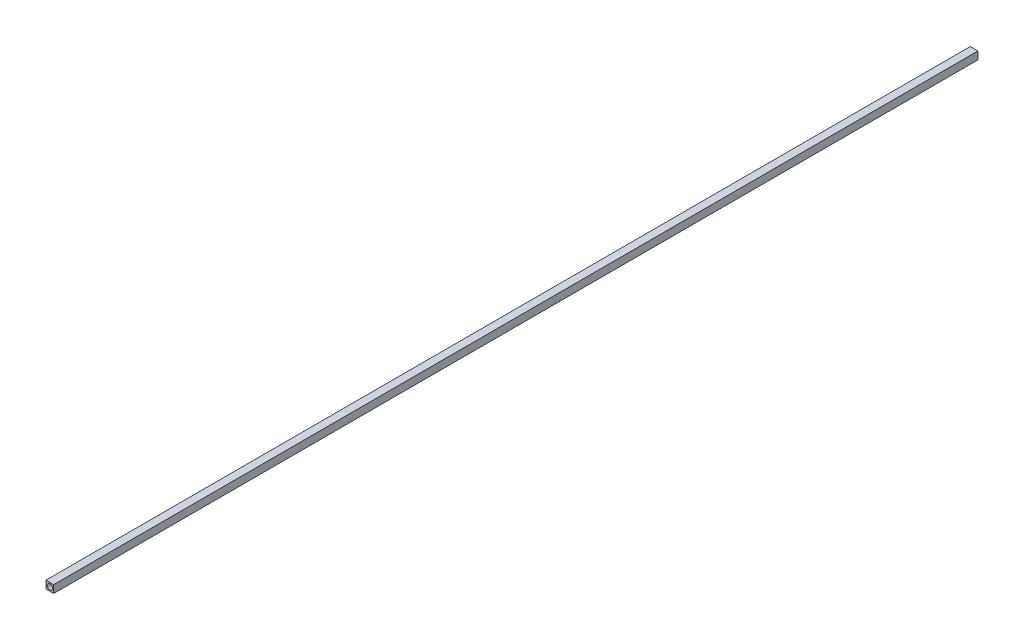
SolidWorks part; units mm, degrees
material "Uni Pultruded Tube"
ref_plane "Front Plane" through (0, 0, 0) normal (0, 0, 1) x (1, 0, 0)
ref_plane "Top Plane" through (0, 0, 0) normal (0, 1, 0) x (1, 0, 0)
ref_plane "Right Plane" through (0, 0, 0) normal (1, 0, 0) x (0, 0, -1)
sketch "Sketch1" plane through (0, 0, 0) normal (0, 0, 1) x (1, 0, 0)
  line L1 (3.175, -3.175) -> (-3.175, -3.175)
  line L2 (3.175, -3.175) -> (3.175, 3.175)
  line L3 (3.175, 3.175) -> (-3.175, 3.175)
  line L4 (-3.175, -3.175) -> (-3.175, 3.175)
  line L5 (3.175, -3.175) -> (-3.175, 3.175) construction
  line L6 (3.175, 3.175) -> (-3.175, -3.175) construction
  circle A0 centre (0, 0) radius 2.1844
  point P0 (0, 0)
  dimension "D3" = 4.3688
  dimension "D1" = 6.35
  dimension "D2" = 6.35
extrude "Boss-Extrude1" add sketch "Sketch1" along normal blind 762
